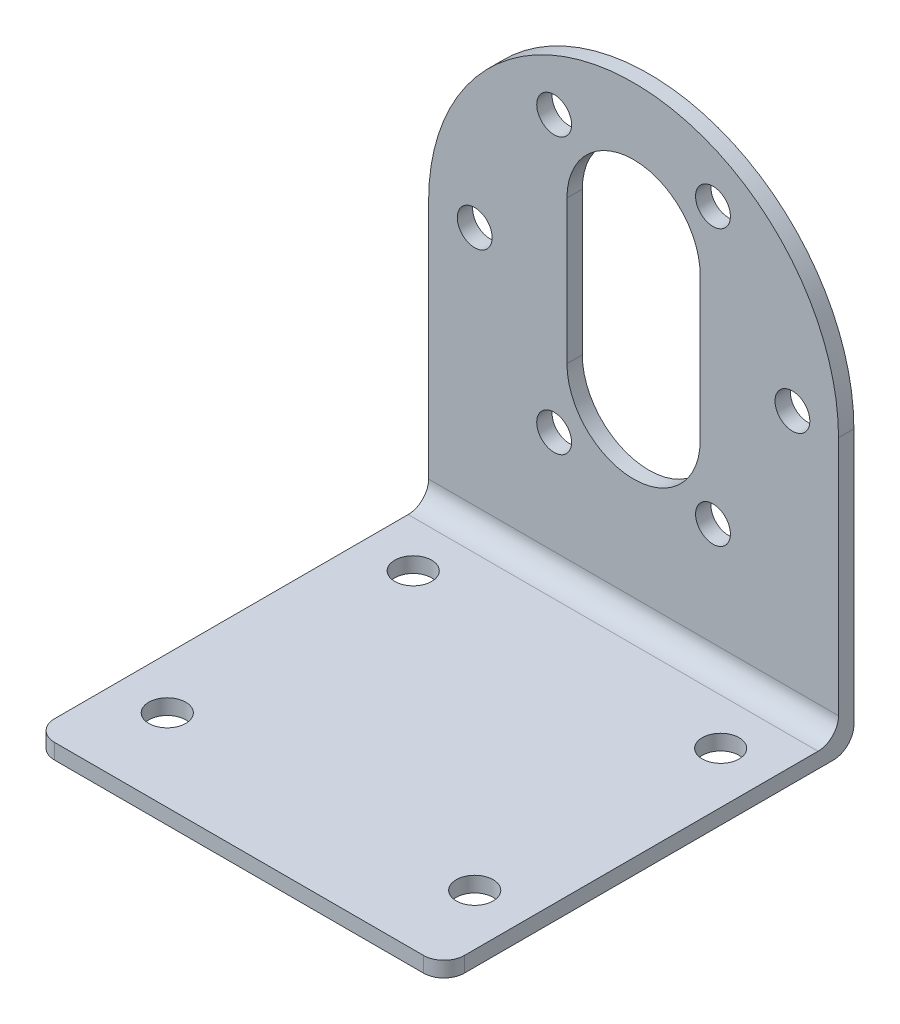
SolidWorks part; units mm, degrees
ref_plane "Front Plane" through (0, 0, 0) normal (0, 0, 1) x (1, 0, 0)
ref_plane "Top Plane" through (0, 0, 0) normal (0, 1, 0) x (1, 0, 0)
ref_plane "Right Plane" through (0, 0, 0) normal (1, 0, 0) x (0, 0, -1)
sketch "Sketch1" plane through (0, 0, 0) normal (0, 1, 0) x (1, 0, 0)
  line L1 (0, 0) -> (40, 0)
  line L2 (0, 0) -> (0, 40)
  line L3 (0, 40) -> (40, 40)
  line L4 (40, 0) -> (40, 40)
  dimension "D1" = 40
  dimension "D2" = 40
extrude "Boss-Extrude1" add sketch "Sketch1" along normal blind 1.5
sketch "Sketch2" plane through (0, 1.5, 0) normal (0, 1, 0) x (1, 0, 0)
  line L0 (40, 0) -> (40, 40) construction
  line L1 (0, 40) -> (40, 40)
  line L2 (0, 40) -> (0, 38.5)
  line L3 (0, 38.5) -> (40, 38.5)
  line L4 (40, 40) -> (40, 38.5)
  dimension "D1" = 1.5
extrude "Boss-Extrude2" add sketch "Sketch2" along normal blind 45.5
sketch "Sketch3" plane through (0, 0, -40) normal (0, 0, -1) x (-1, 0, 0)
  line L0 (-20, 47) -> (-20, 0) construction
  line L1 (-40, 47) -> (0, 47) construction
  line L2 (-40, 0) -> (0, 0) construction
  line L3 (-20, 34) -> (-20, 20) construction
  line L4 (-13.5, 34) -> (-13.5, 20)
  line L5 (-26.5, 34) -> (-26.5, 20)
  line L6 (-40, 27) -> (0, 27) construction
  line L7 (-40, 47) -> (-40, 0) construction
  line L8 (0, 47) -> (0, 0) construction
  arc A0 (-13.5, 34) -> (-26.5, 34) centre (-20, 34) ccw
  arc A1 (-26.5, 20) -> (-13.5, 20) centre (-20, 20) ccw
  arc A4 (0, 27) -> (-40, 27) centre (-20, 27) ccw
  point P8 (-20, 27)
  dimension "D1" = 13
  dimension "D2" = 14
  dimension "D3" = 20
extrude "Cut-Extrude2" cut sketch "Sketch3" against normal up to next contours A4 L8 A0 | L5 A1 L4 A0 | A4 L7 L8
sketch "Sketch4" plane through (0, 0, -40) normal (0, 0, -1) x (-1, 0, 0)
  line L0 (-20, 0) -> (-20, 47) construction
  line L1 (-40, 0) -> (0, 0) construction
  line L2 (0, 27) -> (-40, 27) construction
  arc A0 (0, 27) -> (-40, 27) centre (-20, 27) ccw construction
  circle A1 centre (-20, 27) radius 15.5 construction
  circle A2 centre (-35.5, 27) radius 1.7
  circle A3 centre (-27.75, 40.4234) radius 1.7
  circle A4 centre (-12.25, 40.4234) radius 1.7
  circle A5 centre (-4.5, 27) radius 1.7
  circle A6 centre (-12.25, 13.5766) radius 1.7
  circle A7 centre (-27.75, 13.5766) radius 1.7
  point P27 (-20, 27)
  dimension "D1" = 31
  dimension "D2" = 3.4
  dimension "D3" = 6
extrude "Cut-Extrude3" cut sketch "Sketch4" against normal up to next
sketch "Sketch5" plane through (0, 1.5, 0) normal (0, 1, 0) x (1, 0, 0)
  line L0 (0, 0) -> (40, 0) construction
  line L1 (5, 32) -> (35, 32) construction
  line L2 (5, 32) -> (5, 8) construction
  line L3 (5, 8) -> (35, 8) construction
  line L4 (35, 32) -> (35, 8) construction
  line L5 (0, 38.5) -> (0, 0) construction
  circle A0 centre (5, 32) radius 1.8
  circle A1 centre (35, 32) radius 1.8
  circle A2 centre (35, 8) radius 1.8
  circle A3 centre (5, 8) radius 1.8
  dimension "D5" = 3.6
  dimension "D6" = 3.6
  dimension "D7" = 3.6
  dimension "D8" = 3.6
  dimension "D1" = 30
  dimension "D2" = 24
  dimension "D3" = 8
  dimension "D4" = 5
extrude "Cut-Extrude4" cut sketch "Sketch5" against normal up to next
fillet "Fillet1" radius 2 4 edges at (20, 1.5, -38.5) (20, 0, -40) (40, 0.75, 0) (0, 0.75, 0)
sketch "Sketch6" plane through (0, 0, 0) normal (0, -1, 0) x (1, 0, 0)
  line L0 (20, 0) -> (20, -38) construction
  line L1 (2, 0) -> (38, 0) construction
  line L2 (0, -38) -> (40, -38) construction
